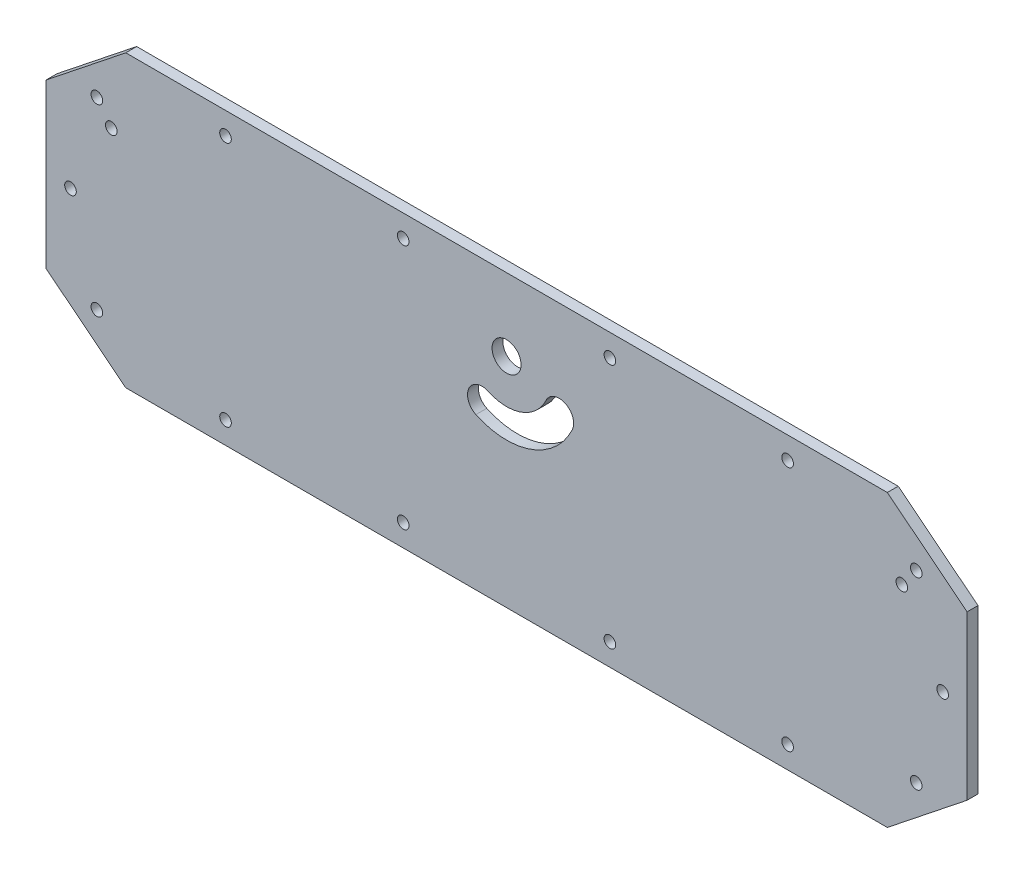
SolidWorks part; units mm, degrees
ref_plane "Alzado" through (0, 0, 0) normal (0, 0, 1) x (1, 0, 0)
ref_plane "Planta" through (0, 0, 0) normal (0, 1, 0) x (1, 0, 0)
ref_plane "Vista lateral" through (0, 0, 0) normal (1, 0, 0) x (0, 0, -1)
sketch "Croquis1" plane through (0, 0, 0) normal (0, 0, 1) x (1, 0, 0)
  line L0 (-127, 22.5) -> (-105, 40)
  line L1 (127, -40) -> (-127, -40) construction
  line L2 (127, -40) -> (127, 40) construction
  line L3 (127, 40) -> (-127, 40) construction
  line L4 (-127, -40) -> (-127, 40) construction
  line L5 (127, -40) -> (-127, 40) construction
  line L6 (127, 40) -> (-127, -40) construction
  line L7 (-105, 40) -> (105, 40)
  line L8 (105, 40) -> (127, 22.5)
  line L9 (127, 22.5) -> (127, -22.5)
  line L10 (127, -22.5) -> (105, -40)
  line L11 (105, -40) -> (-105, -40)
  line L12 (-105, -40) -> (-127, -22.5)
  line L13 (-127, -22.5) -> (-127, 22.5)
  line L14 (0, -40) -> (0, 40) construction
  line L15 (0, 33.9) -> (-28.5, 33.9) construction
  line L16 (-28.5, 33.9) -> (-77.5, 33.9) construction
  line L17 (0, 33.9) -> (28.5, 33.9) construction
  line L18 (28.5, 33.9) -> (77.5, 33.9) construction
  line L19 (0, -33.9) -> (-28.5, -33.9) construction
  line L20 (-28.5, -33.9) -> (-77.5, -33.9) construction
  line L21 (0, -33.9) -> (28.5, -33.9) construction
  line L22 (28.5, -33.9) -> (77.5, -33.9) construction
  line L23 (-127, 0) -> (-120.25, 0) construction
  line L24 (127, 0) -> (120.25, 0) construction
  line L25 (5.4723, 4.9649) -> (0, 20) construction
  line L26 (-112.98, -25.35) -> (112.98, -25.35) construction
  line L27 (-112.98, -25.35) -> (-112.98, 25.35) construction
  line L28 (-112.98, 25.35) -> (112.98, 25.35) construction
  line L29 (112.98, -25.35) -> (112.98, 25.35) construction
  line L30 (-112.98, -25.35) -> (112.98, 25.35) construction
  line L31 (-112.98, 25.35) -> (112.98, -25.35) construction
  line L32 (0, 20) -> (-6.7619, 5.4991) construction
  line L33 (0, 20) -> (14.5009, 13.2381) construction
  line L34 (0, 20) -> (-109, 20) construction
  line L35 (0, 20) -> (109, 20) construction
  circle A0 centre (0, 20) radius 4
  circle A1 centre (112.98, 25.35) radius 1.6
  circle A2 centre (120.25, 0) radius 1.6
  circle A3 centre (112.98, -25.35) radius 1.6
  circle A4 centre (77.5, -33.9) radius 1.6
  circle A5 centre (28.5, -33.9) radius 1.6
  circle A6 centre (-28.5, -33.9) radius 1.6
  circle A7 centre (-77.5, -33.9) radius 1.6
  circle A8 centre (-112.98, -25.35) radius 1.6
  circle A9 centre (-120.25, 0) radius 1.6
  circle A10 centre (-112.98, 25.35) radius 1.6
  circle A11 centre (-77.5, 33.9) radius 1.6
  circle A12 centre (-28.5, 33.9) radius 1.6
  circle A13 centre (28.5, 33.9) radius 1.6
  circle A14 centre (77.5, 33.9) radius 1.6
  arc A15 (-6.7619, 5.4991) -> (14.5009, 13.2381) centre (0, 20) ccw construction
  arc A16 (-8.4524, 1.8738) -> (18.1262, 11.5476) centre (0, 20) ccw
  arc A17 (-5.0714, 9.1243) -> (10.8757, 14.9286) centre (0, 20) ccw
  arc A18 (-5.0714, 9.1243) -> (-8.4524, 1.8738) centre (-6.7619, 5.4991) ccw
  arc A19 (18.1262, 11.5476) -> (10.8757, 14.9286) centre (14.5009, 13.2381) ccw
  circle A20 centre (-109, 20) radius 1.6
  circle A21 centre (109, 20) radius 1.6
  point P0 (0, 0)
  point P34 (0, 0)
  point P53 (5.4723, 4.9649)
  dimension "D10" = 8
  dimension "D19" = 3.2
  dimension "D21" = 16
  dimension "D22" = 4
  dimension "D1" = 254
  dimension "D2" = 80
  dimension "D3" = 22
  dimension "D4" = 22
  dimension "D5" = 22
  dimension "D6" = 22
  dimension "D7" = 17.5
  dimension "D8" = 17.5
  dimension "D9" = 17.5
  dimension "D11" = 20
  dimension "D12" = 57
  dimension "D13" = 6.1
  dimension "D14" = 6.1
  dimension "D15" = 49
  dimension "D16" = 6.75
  dimension "D17" = 7.98
  dimension "D18" = 2.85
  dimension "D20" = 90
  dimension "D23" = 20
  dimension "D24" = 109
extrude "Saliente-Extruir1" add sketch "Croquis1" along normal blind 3
